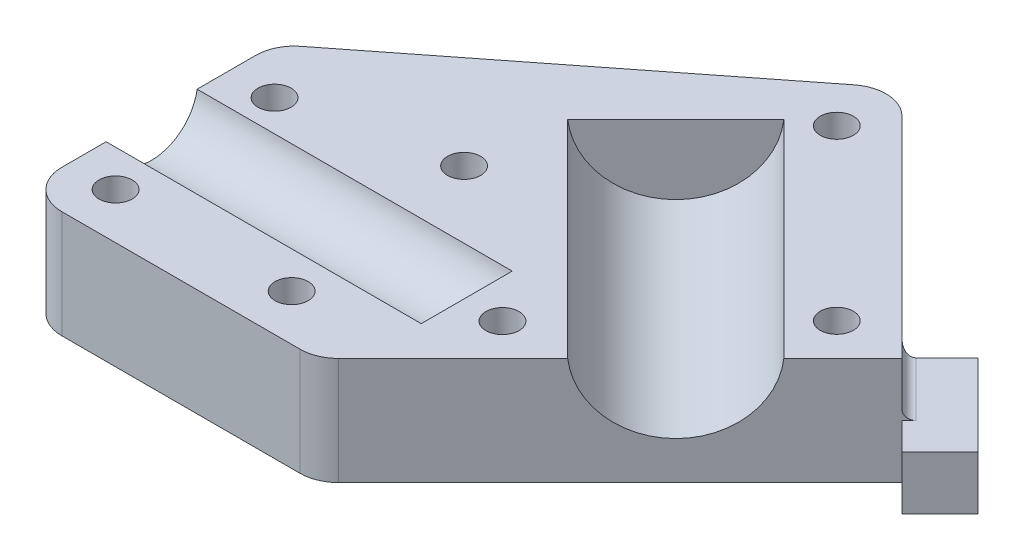
SolidWorks part; units mm, degrees
ref_plane "前视基准面" through (0, 0, 0) normal (0, 0, 1) x (1, 0, 0)
ref_plane "上视基准面" through (0, 0, 0) normal (0, 1, 0) x (1, 0, 0)
ref_plane "右视基准面" through (0, 0, 0) normal (1, 0, 0) x (0, 0, -1)
ref_plane "基准面4" through (0, -15, 0) normal (0, -1, 0) x (1, 0, 0)
sketch "草图1" plane through (0, -15, 0) normal (0, -1, 0) x (1, 0, 0)
  line L0 (4.7435, -52.275) -> (35.2198, -21.7987)
  line L1 (35.2198, -21.7987) -> (-2.9289, 16.35)
  line L2 (-2.9289, 16.35) -> (-41.0289, 16.35)
  line L3 (-41.0289, 16.35) -> (-41.0289, -16.35)
  line L4 (-41.0289, -16.35) -> (4.7435, -52.275)
extrude "凸台-拉伸1" add sketch "草图1" against normal blind 14
sketch "草图2" plane through (0, -15, 0) normal (0, -1, 0) x (1, 0, 0)
  line L0 (43.705, -23.2129) -> (38.7553, -18.2632)
  line L1 (38.7553, -18.2632) -> (35.2198, -21.7987)
  line L2 (35.2198, -21.7987) -> (28.1487, -28.8698)
  line L3 (28.1487, -28.8698) -> (33.0984, -33.8195)
  line L4 (33.0984, -33.8195) -> (43.705, -23.2129)
extrude "凸台-拉伸2" add sketch "草图2" against normal blind 7
sketch "草图3" plane through (-41.0289, 0, 0) normal (-1, 0, 0) x (0, 0, 1)
  line L0 (5.5795, -1) -> (-6.2708, -1)
  arc A0 (-6.2708, -1) -> (5.5795, -1) centre (-0.3456, -0.0551) ccw
extrude "切除-拉伸1" cut sketch "草图3" against normal blind 41.0289
sketch "草图4" plane through (6.7105, 0, 6.7105) normal (0.7071, 0, 0.7071) x (0.7071, 0, -0.7071)
  line L0 (29.4458, -1) -> (9.5383, -1)
  arc A0 (9.5383, -1) -> (29.4458, -1) centre (19.492, -0.0398) ccw
extrude "切除-拉伸2" cut sketch "草图4" against normal blind 38.1
ref_plane "基准面5" through (0, -12, 0) normal (0, -1, 0) x (1, 0, 0)
ref_plane "基准面6" through (0, -17, 0) normal (0, 1, 0) x (1, 0, 0)
hole_wizard "M4 间隙孔1" positions "草图16" profile "草图15" hole size "M4" standard "ANSI Metric"
sketch "草图16" plane through (0, -15, 0) normal (0, -1, 0) x (-1, 0, 0)
  point P0 (35.0289, -10.35)
  point P1 (-5, 0)
  point P2 (15, 15)
  point P3 (12.103, -10.35)
  point P4 (35.0289, 10.35)
  point P5 (-4.7435, 43.7897)
  point P6 (-26.7345, 21.7987)
sketch "草图15" plane through (-35.0289, -15, 10.35) normal (1, 0, 0) x (0, 0, -1)
  line L0 (0, 0) -> (0, 14)
  line L1 (0, 14) -> (2.159, 14)
  line L2 (2.159, 14) -> (2.159, 0)
  line L5 (2.159, 0) -> (0, 0)
  line L11 (0, -6.35) -> (0, 107.95) construction
  dimension "通孔孔直径" = 4.318
  dimension "通孔孔深度" = 14
fillet "圆角1" radius 5 4 edges at (-41.0289, -8, 16.35) (-2.9289, -8, 16.35) (-41.0289, -8, -16.35) (4.7435, -8, -52.275)
fillet "圆角3" radius 1.27 1 edges at (31.6842, -8, -25.3342)
fillet "圆角4" radius 1.27 1 edges at (28.1487, -10.865, -28.8698)
